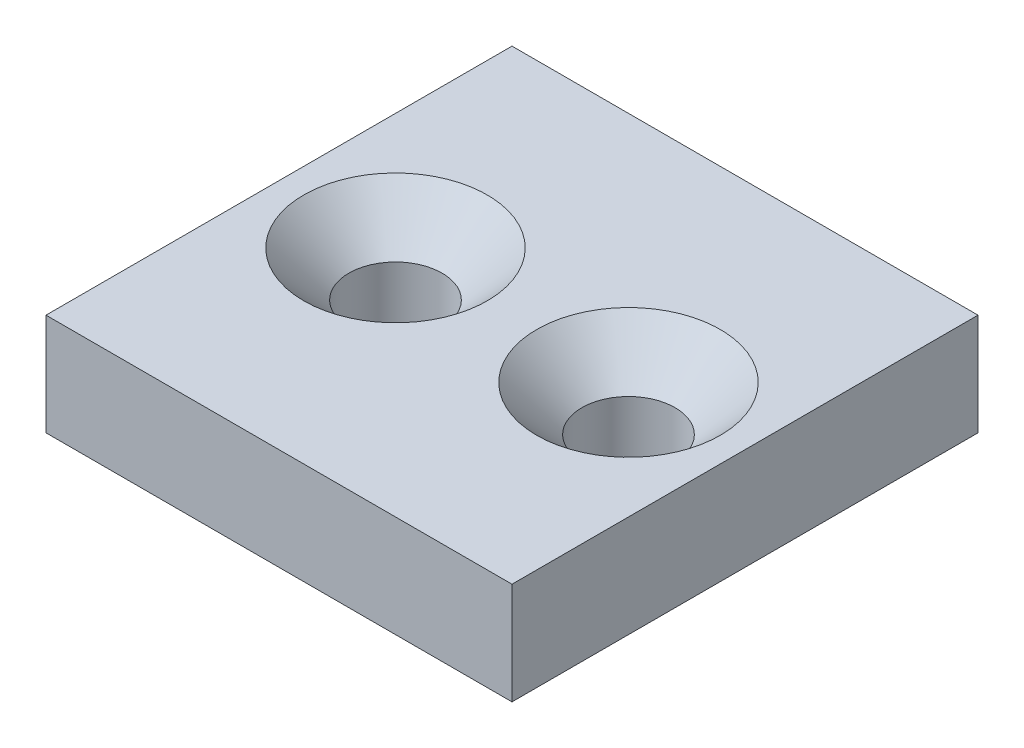
SolidWorks part; units mm, degrees
ref_plane "Front Plane" through (0, 0, 0) normal (0, 0, 1) x (1, 0, 0)
ref_plane "Top Plane" through (0, 0, 0) normal (0, 1, 0) x (1, 0, 0)
ref_plane "Right Plane" through (0, 0, 0) normal (1, 0, 0) x (0, 0, -1)
sketch "Sketch1" plane through (0, 0, 0) normal (0, 1, 0) x (1, 0, 0)
  line L1 (-16, 16) -> (16, 16)
  line L2 (-16, 16) -> (-16, -16)
  line L3 (-16, -16) -> (16, -16)
  line L4 (16, 16) -> (16, -16)
  line L5 (-16, 16) -> (16, -16) construction
  line L6 (-16, -16) -> (16, 16) construction
  point P0 (0, 0)
  dimension "D1" = 32
  dimension "D2" = 32
extrude "Boss-Extrude1" add sketch "Sketch1" along normal blind 7
hole_wizard "Hole1" positions "Sketch2" profile "Sketch3" legacy
sketch "Sketch2" plane through (0, 7, 0) normal (0, 1, 0) x (1, 0, 0)
  line L0 (-16, 16) -> (-16, -16) construction
  point P0 (8, 0)
  point P2 (-8, 0)
  point P6 (0, 0)
  point P9 (0, 0)
  dimension "D1" = 16
  dimension "D2" = 8
sketch "Sketch3" plane through (8, 7, 0) normal (1, 0, 0) x (0, 0, 1)
  line L0 (0, 0) -> (0, 7)
  line L1 (0, 7) -> (3.2, 7)
  line L2 (3.2, 7) -> (3.2, 3.1)
  line L3 (3.2, 3.1) -> (6.3, 0)
  line L4 (6.3, 0) -> (0, 0)
  line L5 (0, -14.3089) -> (0, 102.4216) construction
  line L6 (0, 7) -> (-3.2, 7) construction
  line L7 (-3.2, 3.1) -> (-6.3, 0) construction
  dimension "Diameter" = 6.4
  dimension "Depth" = 7
  dimension "C-Sink Diameter" = 12.6
  dimension "C-Sink Angle" = 90
  dimension "Drill Angle" = 180
